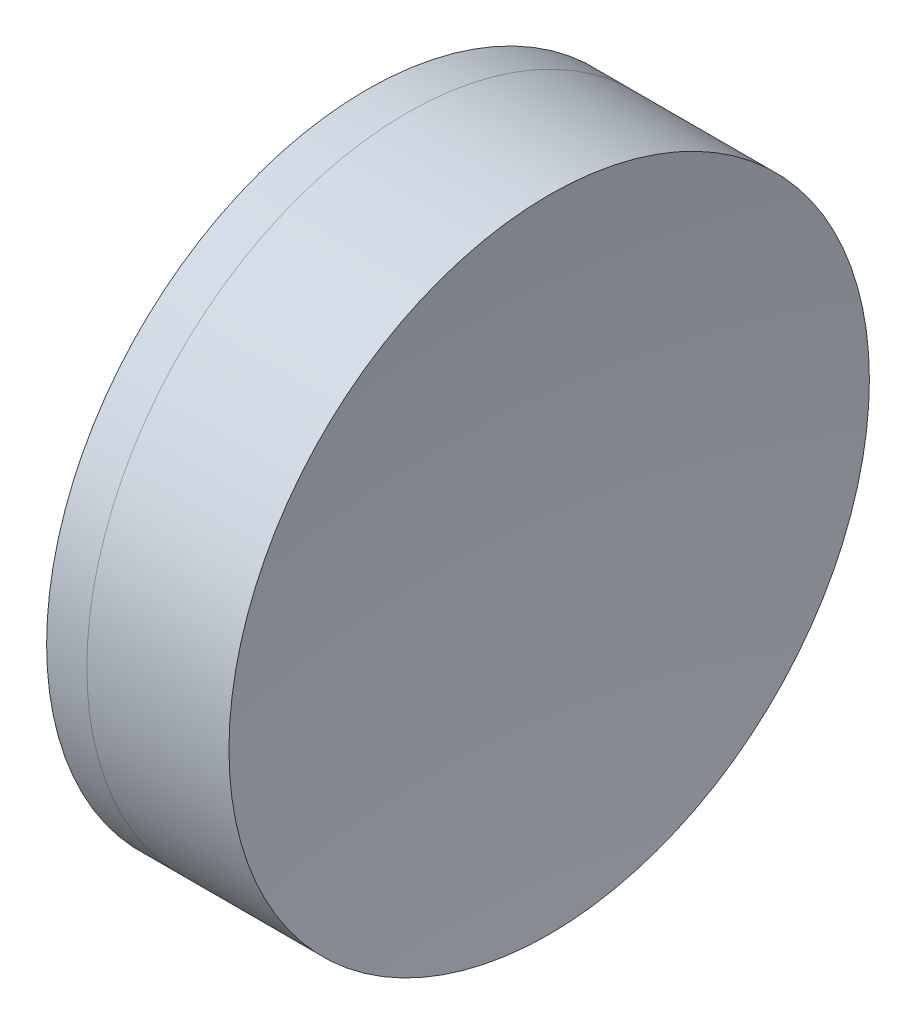
SolidWorks part; units mm, degrees
ref_plane "前视基准面" through (0, 0, 0) normal (0, 0, 1) x (1, 0, 0)
ref_plane "上视基准面" through (0, 0, 0) normal (0, 1, 0) x (1, 0, 0)
ref_plane "右视基准面" through (0, 0, 0) normal (1, 0, 0) x (0, 0, -1)
sketch "草图1" plane through (0, 0, 0) normal (0, 1, 0) x (1, 0, 0)
  line L0 (-0.8161, 0) -> (118.0272, 0) construction
  line L1 (96.5907, -15) -> (98.4749, -15)
  line L2 (96.5907, 15) -> (98.4749, 15)
  arc A0 (98.4749, -15) -> (98.4749, 15) centre (68.063, 0) ccw
  arc A1 (96.5907, 15) -> (96.5907, -15) centre (121.853, 0) ccw
  point P10 (92.473, 0)
  point P11 (101.973, 0)
  dimension "D3" = 29.38
  dimension "D4" = 33.91
  dimension "D1" = 15
  dimension "D2" = 15
  dimension "D5" = 9.5
revolve "旋转1" add sketch "草图1" angle 360 about L0
sketch "草图2" plane through (0, 0, 0) normal (0, 1, 0) x (1, 0, 0)
  line L0 (-0.5519, 0) -> (162.8134, 0) construction
  line L2 (98.4749, 15) -> (105.1311, 15)
  line L3 (98.4749, -15) -> (105.1311, -15)
  arc A0 (105.1311, 15) -> (105.1311, -15) centre (201.693, 0) ccw
  arc A1 (98.4749, -15) -> (98.4749, 15) centre (68.063, 0) ccw construction
  arc A2 (98.4749, -15) -> (98.4749, 15) centre (68.063, 0) ccw
  point P4 (101.973, 0)
  point P8 (103.973, 0)
  dimension "D1" = 97.72
  dimension "D2" = 2
revolve "旋转2" add sketch "草图2" angle 360 about L0
